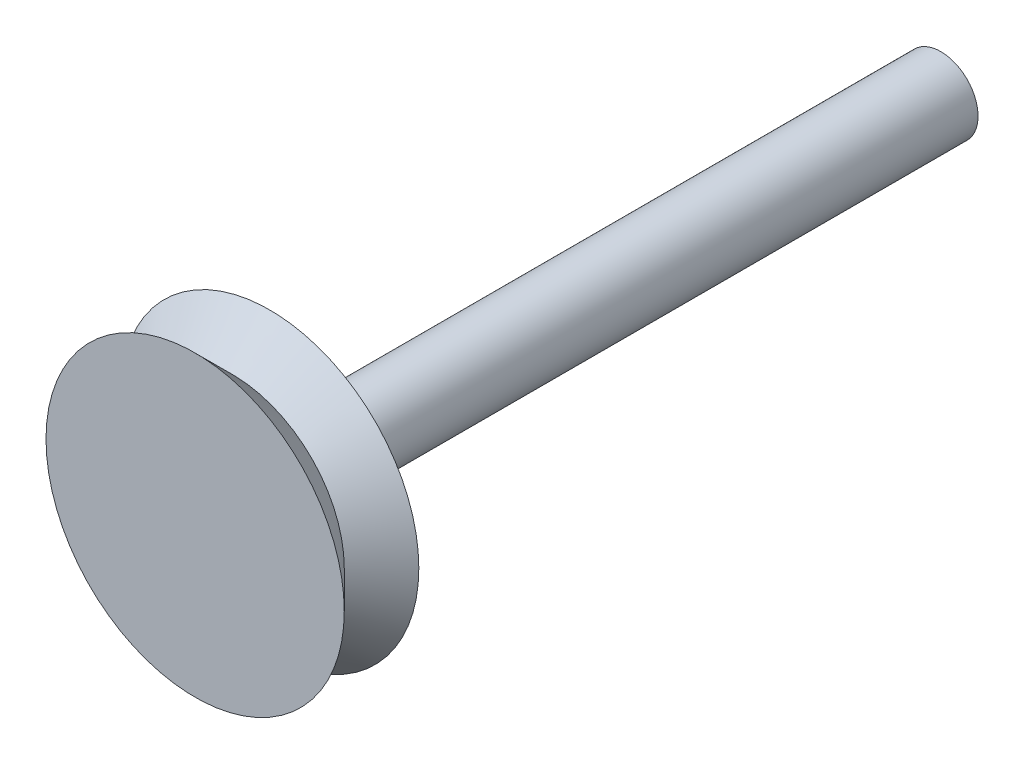
SolidWorks part; units mm, degrees
ref_plane "Front Plane" through (0, 0, 0) normal (0, 0, 1) x (1, 0, 0)
ref_plane "Top Plane" through (0, 0, 0) normal (0, 1, 0) x (1, 0, 0)
ref_plane "Right Plane" through (0, 0, 0) normal (1, 0, 0) x (0, 0, -1)
sketch "Sketch1" plane through (0, 0, 0) normal (0, 0, 1) x (1, 0, 0)
  circle A0 centre (0, 0) radius 4
extrude "Boss-Extrude1" add sketch "Sketch1" along normal blind 2
sketch "Sketch2" plane through (0, 0, 0) normal (0, 0, -1) x (-1, 0, 0)
  circle A0 centre (0, 0) radius 1
extrude "Boss-Extrude2" add sketch "Sketch2" along normal blind 18
sketch "Sketch3" plane through (0, 0, 0) normal (1, 0, 0) x (0, 0, -1)
  line L0 (-2, 4) -> (-1, 3)
  line L1 (-1, 3) -> (0, 4)
  line L2 (0, 4) -> (-2, 4)
  line L3 (-1, 2.3836) -> (-1, 4.4359) construction
  line L4 (-3.1151, 0) -> (19.3859, 0) construction
  dimension "D1" = 90
revolve "Cut-Revolve1" cut sketch "Sketch3" angle 360 about L4
